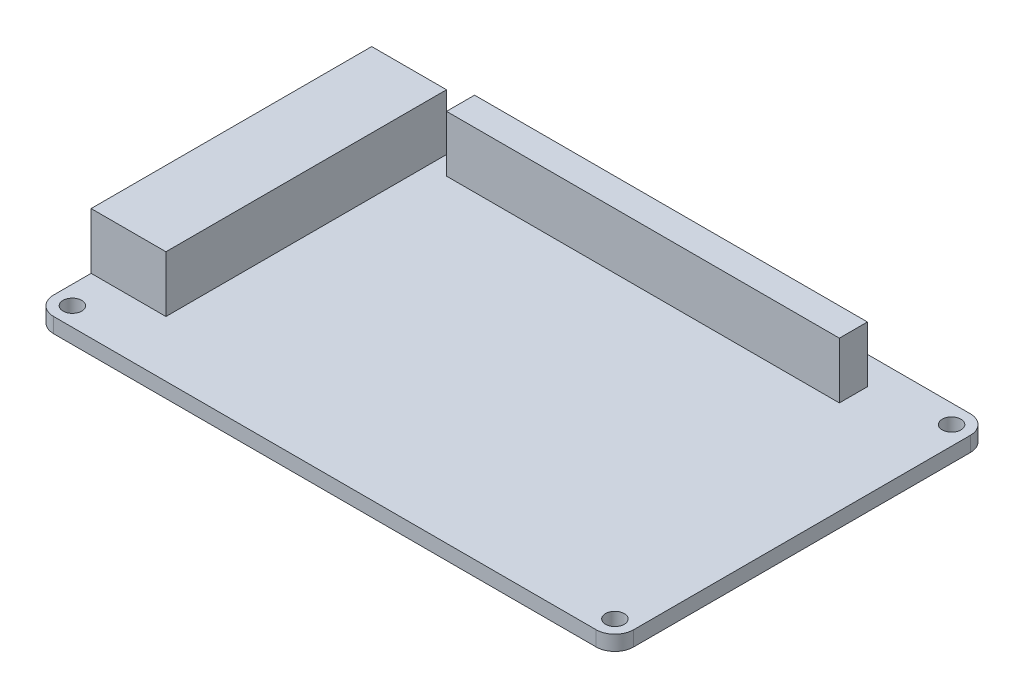
SolidWorks part; units mm, degrees
ref_plane "Front Plane" through (0, 0, 0) normal (0, 0, 1) x (1, 0, 0)
ref_plane "Top Plane" through (0, 0, 0) normal (0, 1, 0) x (1, 0, 0)
ref_plane "Right Plane" through (0, 0, 0) normal (1, 0, 0) x (0, 0, -1)
sketch "Sketch1" plane through (0, 0, 0) normal (0, 1, 0) x (1, 0, 0)
  line L0 (0, 0) -> (0, 19.4425) construction
  line L1 (-46.0375, 31.75) -> (46.0375, 31.75)
  line L2 (-49.2125, 28.575) -> (-49.2125, -28.575)
  line L3 (-46.0375, -31.75) -> (46.0375, -31.75)
  line L4 (49.2125, 28.575) -> (49.2125, -28.575)
  line L5 (-49.2125, 31.75) -> (49.2125, -31.75) construction
  line L6 (-49.2125, -31.75) -> (49.2125, 31.75) construction
  line L7 (0, 0) -> (13.1782, 0) construction
  arc A0 (46.0375, 31.75) -> (49.2125, 28.575) centre (46.0375, 28.575) cw
  arc A1 (46.0375, -31.75) -> (49.2125, -28.575) centre (46.0375, -28.575) ccw
  arc A2 (-49.2125, -28.575) -> (-46.0375, -31.75) centre (-46.0375, -28.575) ccw
  arc A3 (-46.0375, 31.75) -> (-49.2125, 28.575) centre (-46.0375, 28.575) ccw
  circle A5 centre (-46.0375, 28.575) radius 1.5875
  circle A6 centre (46.0375, 28.575) radius 1.5875
  circle A7 centre (46.0375, -28.575) radius 1.5875
  circle A8 centre (-46.0375, -28.575) radius 1.5875
  point P0 (0, 0)
  dimension "D3" = 3.175
  dimension "D6" = 3.175
  dimension "D1" = 98.425
  dimension "D2" = 63.5
extrude "MainPCB" add sketch "Sketch1" along normal blind 2.54
sketch "Sketch2" plane through (0, 2.54, 0) normal (0, 1, 0) x (1, 0, 0)
  line L0 (-49.2125, 28.575) -> (-49.2125, -28.575) construction
  line L1 (-49.2125, 25.4) -> (-36.5125, 25.4)
  line L2 (-49.2125, 25.4) -> (-49.2125, -22.225)
  line L3 (-49.2125, -22.225) -> (-36.5125, -22.225)
  line L4 (-36.5125, 25.4) -> (-36.5125, -22.225)
  line L5 (46.0375, 31.75) -> (-46.0375, 31.75) construction
  line L6 (-46.0375, -31.75) -> (46.0375, -31.75) construction
  dimension "D1" = 6.35
  dimension "D2" = 9.525
  dimension "D3" = 12.7
extrude "Charger_USBConnections" add sketch "Sketch2" along normal blind 9.525
sketch "Sketch3" plane through (0, 2.54, 0) normal (0, 1, 0) x (1, 0, 0)
  line L0 (49.2125, -28.575) -> (49.2125, 28.575) construction
  line L1 (33.3375, 26.9875) -> (-33.3375, 26.9875)
  line L2 (33.3375, 26.9875) -> (33.3375, 22.225)
  line L3 (33.3375, 22.225) -> (-33.3375, 22.225)
  line L4 (-33.3375, 26.9875) -> (-33.3375, 22.225)
  line L5 (46.0375, 31.75) -> (-46.0375, 31.75) construction
  dimension "D1" = 15.875
  dimension "D2" = 82.55
  dimension "D3" = 4.7625
  dimension "D4" = 4.7625
extrude "GPIO Header" add sketch "Sketch3" along normal blind 9.525
